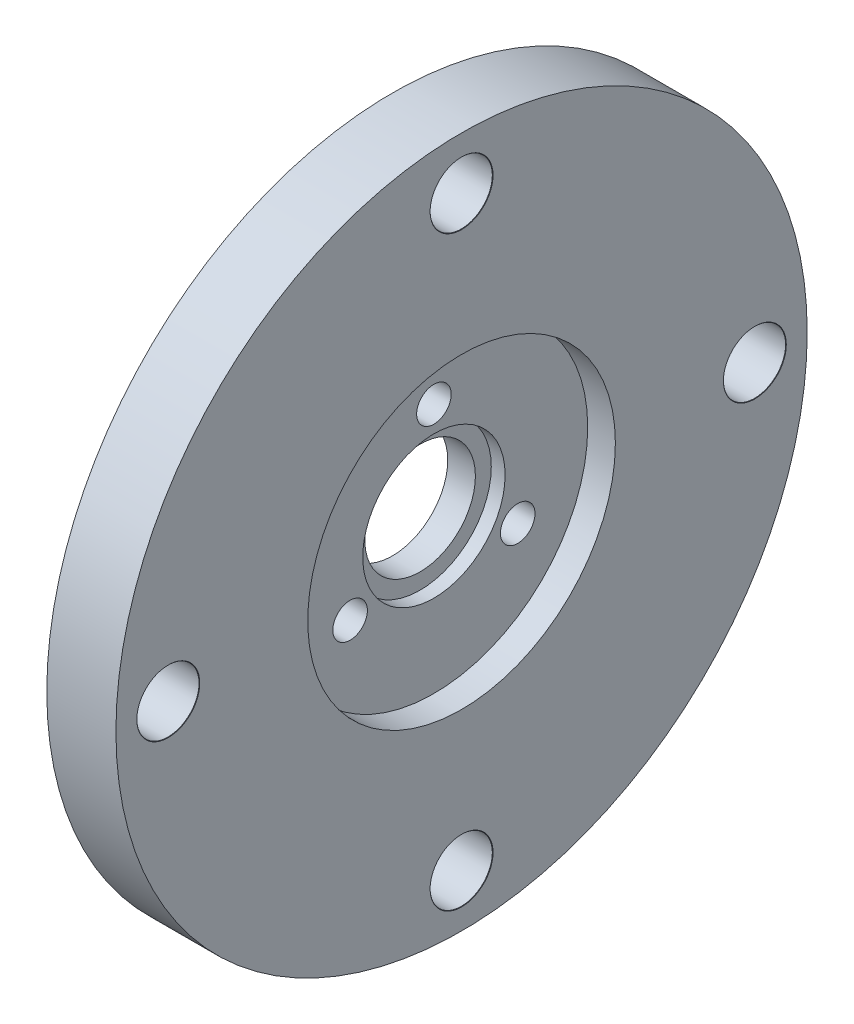
SolidWorks part; units mm, degrees
material "6061-T6 (SS)"
ref_plane "Front Plane" through (0, 0, 0) normal (0, 0, 1) x (1, 0, 0)
ref_plane "Top Plane" through (0, 0, 0) normal (0, 1, 0) x (1, 0, 0)
ref_plane "Right Plane" through (0, 0, 0) normal (1, 0, 0) x (0, 0, -1)
sketch "Sketch1" plane through (0, 0, 0) normal (1, 0, 0) x (0, 0, -1)
  circle A0 centre (0, 0) radius 25
  circle A1 centre (0, 0) radius 4
  dimension "D1" = 50
  dimension "D2" = 8
extrude "Boss-Extrude1" add sketch "Sketch1" along normal blind 5
sketch "Sketch2" plane through (5, 0, 0) normal (1, 0, 0) x (0, 0, -1)
  circle A0 centre (0, 0) radius 5.15
  dimension "D1" = 10.3
extrude "Cut-Extrude1" cut sketch "Sketch2" against normal blind 3
sketch "Sketch3" plane through (5, 0, 0) normal (1, 0, 0) x (0, 0, -1)
  circle A0 centre (0, 0) radius 11.125
  dimension "D1" = 22.25
extrude "Cut-Extrude2" cut sketch "Sketch3" against normal blind 2
sketch "Sketch4" plane through (3, 0, 0) normal (1, 0, 0) x (0, 0, -1)
  line L0 (-6.0622, -3.5) -> (0, 7)
  line L1 (0, 7) -> (6.0622, -3.5)
  line L2 (-6.0622, -3.5) -> (6.0622, -3.5)
  circle A0 centre (0, 0) radius 7
  circle A1 centre (0, 7) radius 1.25
  circle A2 centre (6.0622, -3.5) radius 1.25
  circle A3 centre (-6.0622, -3.5) radius 1.25
  dimension "D1" = 14
  dimension "D2" = 2.5
extrude "Cut-Extrude3" cut sketch "Sketch4" against normal through all contours A0 A1 | A0 A1 L0 | L1 A1 A0 | L0 A1 L1 | L1 A2 L2 | A0 A2 L1 | L2 A2 A0 | A0 A2 | A0 A3 L2 | L2 A3 L0 | L0 A3 A0 | A0 A3
sketch "Sketch9" plane through (5, 0, 0) normal (1, 0, 0) x (0, 0, -1)
  line L0 (-21.2132, 0) -> (0, 21.2132)
  line L1 (0, 21.2132) -> (21.2132, 0)
  line L2 (21.2132, 0) -> (0, -21.2132)
  line L3 (0, -21.2132) -> (-21.2132, 0)
  point P0 (0, 21.2132)
  point P2 (21.2132, 0)
  point P4 (-21.2132, 0)
  point P6 (0, -21.2132)
  point P18 (-19.1765, -0.1403)
  point P19 (0, 0)
  point P21 (0.1688, -19.0921)
  point P22 (0, 0)
  dimension "D1" = 30
hole_wizard "M4 Clearance Hole1" positions "Sketch9" profile "Sketch8" hole size "M4" standard "ANSI Metric"
sketch "Sketch8" plane through (5, 21.2132, 0) normal (0, 1, 0) x (0, 0, -1)
  line L0 (0, 0) -> (0, 8.9519)
  line L1 (0, 8.9519) -> (2.25, 7.6)
  line L2 (2.25, 7.6) -> (2.25, 0.025)
  line L3 (2.25, 0.025) -> (2.275, 0)
  line L5 (2.275, 0) -> (0, 0)
  line L6 (-2.25, 0.025) -> (-2.275, 0) construction
  line L10 (0, 8.9519) -> (-2.25, 7.6) construction
  line L11 (0, -6.35) -> (0, 107.95) construction
  dimension "Hole Dia." = 4.5
  dimension "Hole Depth" = 7.6
  dimension "Near C'Sink Dia." = 4.55
  dimension "Near C'Sink Angle" = 90
  dimension "Drill Angle" = 118
